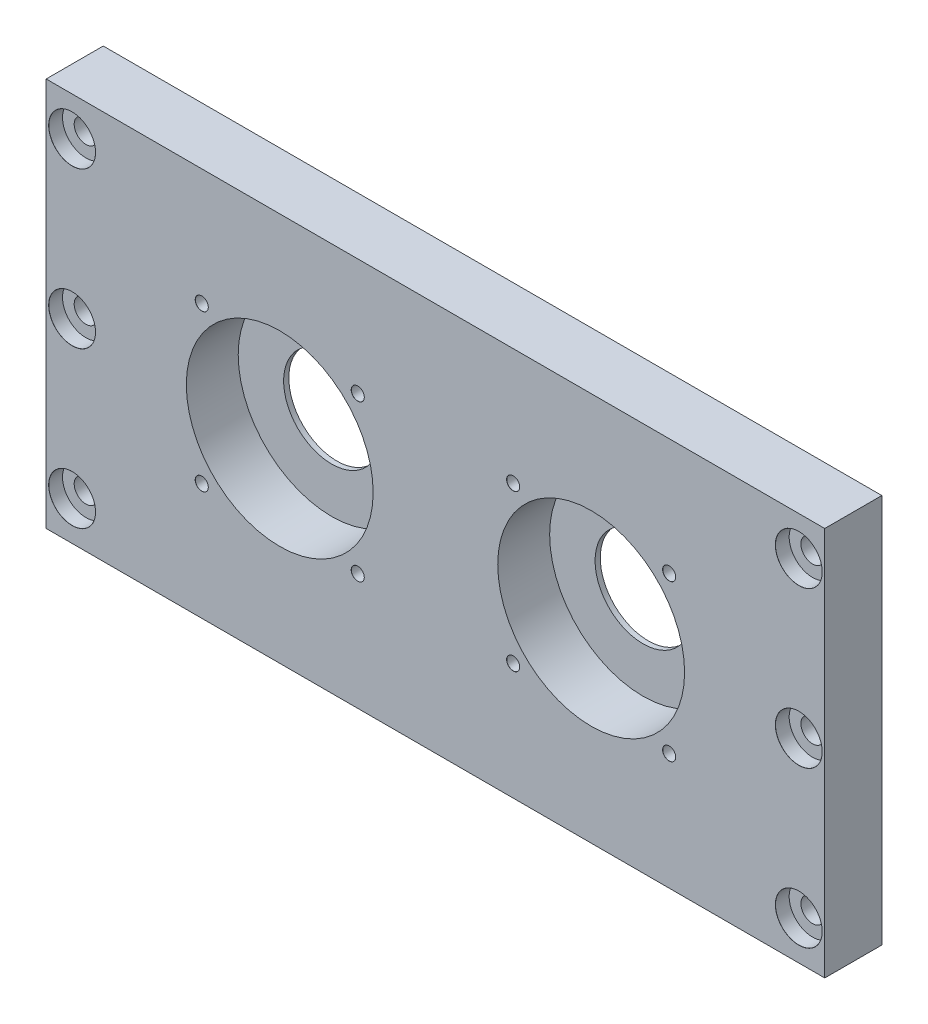
SolidWorks part; units mm, degrees
material "Malleable Cast Iron"
ref_plane "Front Plane" through (0, 0, 0) normal (0, 0, 1) x (1, 0, 0)
ref_plane "Top Plane" through (0, 0, 0) normal (0, 1, 0) x (1, 0, 0)
ref_plane "Right Plane" through (0, 0, 0) normal (1, 0, 0) x (0, 0, -1)
sketch "Sketch1" plane through (0, 0, 0) normal (0, 0, 1) x (1, 0, 0)
  line L1 (-150, 75) -> (150, 75)
  line L2 (-150, 75) -> (-150, -75)
  line L3 (-150, -75) -> (150, -75)
  line L4 (150, 75) -> (150, -75)
  line L5 (-150, 75) -> (150, -75) construction
  line L6 (-150, -75) -> (150, 75) construction
  point P0 (0, 0)
  dimension "D1" = 300
  dimension "D2" = 150
extrude "Boss-Extrude1" add sketch "Sketch1" along normal blind 22
sketch "Sketch2" plane through (0, 0, 22) normal (0, 0, 1) x (1, 0, 0)
  circle A0 centre (-60, 0) radius 36
  dimension "D1" = 72
  dimension "D2" = 60
extrude "Cut-Extrude1" cut sketch "Sketch2" against normal blind 20
sketch "Sketch3" plane through (0, 0, 2) normal (0, 0, 1) x (1, 0, 0)
  circle A0 centre (-60, 0) radius 18.5
  dimension "D1" = 37
extrude "Cut-Extrude2" cut sketch "Sketch3" against normal blind 19
sketch "Sketch4" plane through (0, 0, 22) normal (0, 0, 1) x (1, 0, 0)
  point P0 (-140, 60)
  point P1 (-140, 0)
  point P2 (-140, -60)
  dimension "D1" = 60
  dimension "D2" = 60
  dimension "D3" = 140
hole_wizard "CBORE for M8 Hex Head Bolt1" positions "Sketch5" profile "Sketch6" counterbore size "M8" standard "ISO"
sketch "Sketch5" plane through (0, 0, 22) normal (0, 0, 1) x (1, 0, 0)
  point P0 (-140, 60)
  point P3 (-140, 0)
  point P6 (-140, -60)
sketch "Sketch6" plane through (-140, 60, 22) normal (1, 0, 0) x (0, -1, 0)
  line L0 (0, 0) -> (0, 27.5)
  line L1 (0, 27.5) -> (4.5, 24.7961)
  line L2 (4.5, 24.7961) -> (4.5, 5.3)
  line L3 (4.5, 5.3) -> (9.0055, 5.3)
  line L5 (9.0055, 5.3) -> (9.0055, 0.025)
  line L6 (9.0055, 0.025) -> (9.0305, 0)
  line L7 (9.0305, 0) -> (0, 0)
  line L8 (-9.0055, 0.025) -> (-9.0305, 0) construction
  line L10 (0, 27.5) -> (-4.5, 24.7961) construction
  line L11 (0, -6.35) -> (0, 107.95) construction
  dimension "Hole Dia." = 9
  dimension "Hole Depth" = 27.5
  dimension "C'Bore Dia." = 18.011
  dimension "C'Bore Depth" = 5.3
  dimension "Near C'Sink Dia." = 18.061
  dimension "Near C'Sink Angle" = 90
  dimension "Drill Angle" = 118
mirror "Mirror1" about plane through (0, 0, 0) normal (1, 0, 0) of "Cut-Extrude2", "Cut-Extrude1", "CBORE for M8 Hex Head Bolt1"
sketch "Sketch7" plane through (0, 0, 22) normal (0, 0, 1) x (1, 0, 0)
  line L0 (-60, 0) -> (-29.948, 30.052) construction
  line L1 (-60, 0) -> (0, 0)
  circle A0 centre (-60, 0) radius 42.5 construction
  dimension "D1" = 85
  dimension "D2" = 45
hole_wizard "Tap Drill for M6 Tap1" positions "Sketch8" profile "Sketch9" hole size "M6" standard "ISO"
sketch "Sketch8" plane through (0, 0, 22) normal (0, 0, 1) x (1, 0, 0)
  point P0 (-29.948, 30.052)
sketch "Sketch9" plane through (-29.948, 30.052, 22) normal (1, 0, 0) x (0, -1, 0)
  line L0 (0, 0) -> (0, 27.5)
  line L1 (0, 27.5) -> (2.5, 25.9978)
  line L2 (2.5, 25.9978) -> (2.5, 0.025)
  line L3 (2.5, 0.025) -> (2.525, 0)
  line L5 (2.525, 0) -> (0, 0)
  line L6 (-2.5, 0.025) -> (-2.525, 0) construction
  line L10 (0, 27.5) -> (-2.5, 25.9978) construction
  line L11 (0, -6.35) -> (0, 107.95) construction
  dimension "Hole Dia." = 5
  dimension "Hole Depth" = 27.5
  dimension "Near C'Sink Dia." = 5.05
  dimension "Near C'Sink Angle" = 90
  dimension "Drill Angle" = 118
pattern_circular "CirPattern1" count 4 over 360 about axis through (-60, 0, 0) along (0, 0, 1) of "Tap Drill for M6 Tap1"
mirror "Mirror2" about plane through (0, 0, 0) normal (1, 0, 0) of "CirPattern1", "Tap Drill for M6 Tap1"
